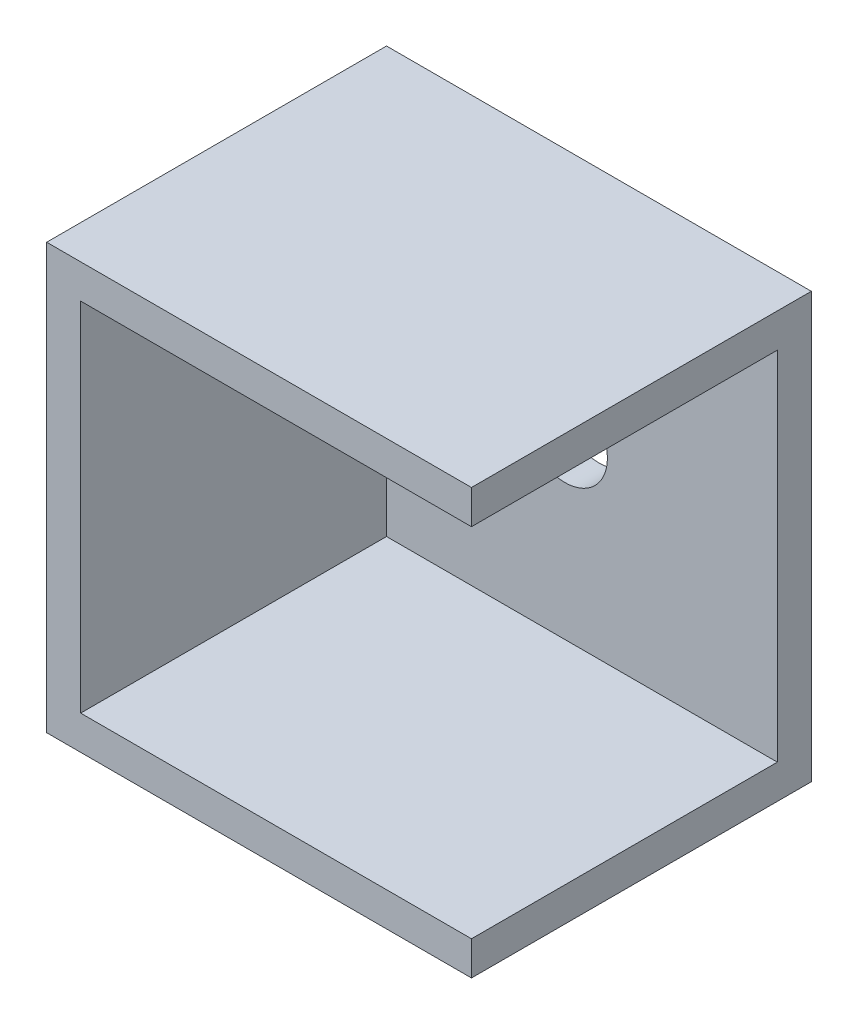
SolidWorks part; units mm, degrees
ref_plane "Ön Düzlem" through (0, 0, 0) normal (0, 0, 1) x (1, 0, 0)
ref_plane "Üst Düzlem" through (0, 0, 0) normal (0, 1, 0) x (1, 0, 0)
ref_plane "Sağ Düzlem" through (0, 0, 0) normal (1, 0, 0) x (0, 0, -1)
sketch "Çizim1" plane through (0, 0, 0) normal (0, 0, 1) x (1, 0, 0)
  line L1 (-12.5, 12.5) -> (12.5, 12.5)
  line L2 (-12.5, 12.5) -> (-12.5, -12.5)
  line L3 (-12.5, -12.5) -> (12.5, -12.5)
  line L4 (12.5, 12.5) -> (12.5, -12.5)
  line L5 (-12.5, 12.5) -> (12.5, -12.5) construction
  line L6 (-12.5, -12.5) -> (12.5, 12.5) construction
  point P0 (0, 0)
  dimension "D1" = 25
  dimension "D2" = 25
extrude "Yükseklik-Ekstrüzyon1" add sketch "Çizim1" along normal blind 20
shell "İç Boşaltma1" thickness 2
sketch "Çizim2" plane through (0, 0, 2) normal (0, 0, 1) x (1, 0, 0)
  circle A0 centre (0, 0) radius 2.5
  dimension "D1" = 5
extrude "Kes-Ekstrüzyon1" cut sketch "Çizim2" against normal blind 5
